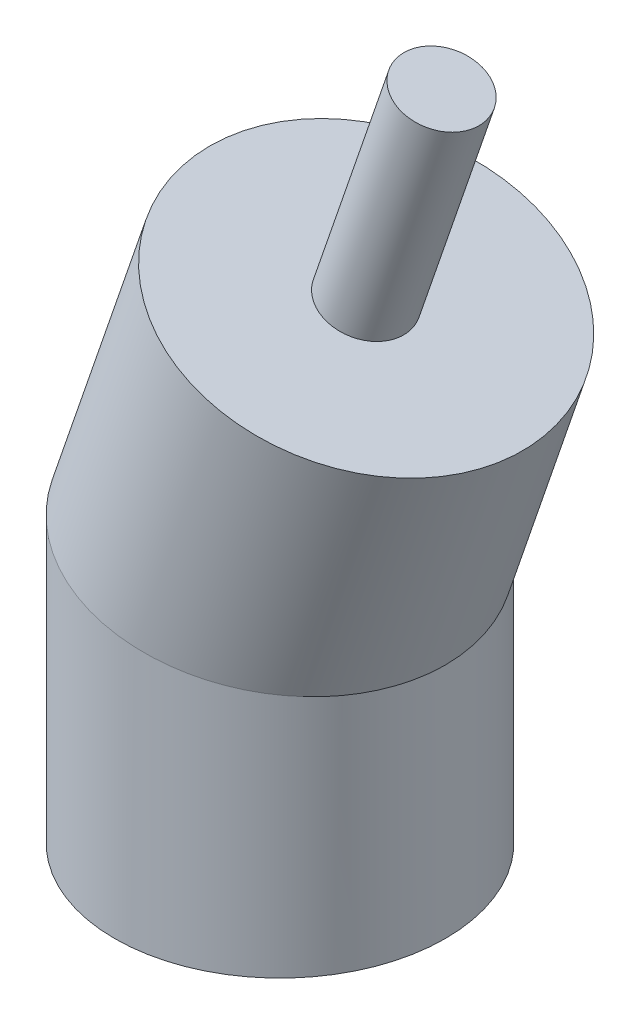
SolidWorks part; units mm, degrees
ref_plane "Plano frontal" through (0, 0, 0) normal (0, 0, 1) x (1, 0, 0)
ref_plane "Plano superior" through (0, 0, 0) normal (0, 1, 0) x (1, 0, 0)
ref_plane "Plano direito" through (0, 0, 0) normal (1, 0, 0) x (0, 0, -1)
sketch "Esboço1" plane through (0, 0, 0) normal (0, 0, 1) x (1, 0, 0)
  line L0 (13.0227, 77.8207) -> (0, 40)
  line L1 (0, 40) -> (0, 0)
  dimension "D1" = 19
  dimension "D2" = 40
  dimension "D3" = 40
sketch "Esboço2" plane through (0, 0, 0) normal (0, 1, 0) x (1, 0, 0)
  circle A0 centre (0, 0) radius 25
  dimension "D1" = 50
sweep "Varredura1" add profiles "Esboço2" path "Esboço1"
sketch "Esboço3" plane through (25.336, 73.581, 0) normal (0.3256, 0.9455, 0) x (0.9455, -0.3256, 0)
  line L0 (-13.0227, 0) -> (0, 0) construction
  circle A0 centre (-13.0227, 0) radius 6
  circle A1 centre (-13.0227, 0) radius 25 construction
  dimension "D1" = 12
extrude "Ressalto-extrusão1" add sketch "Esboço3" along normal blind 35
sketch "Esboço4" plane through (0, 0, 0) normal (0, -1, 0) x (1, 0, 0)
  circle A0 centre (0, 0) radius 6
  dimension "D1" = 12
extrude "Corte-extrusão1" cut sketch "Esboço4" against normal blind 20
